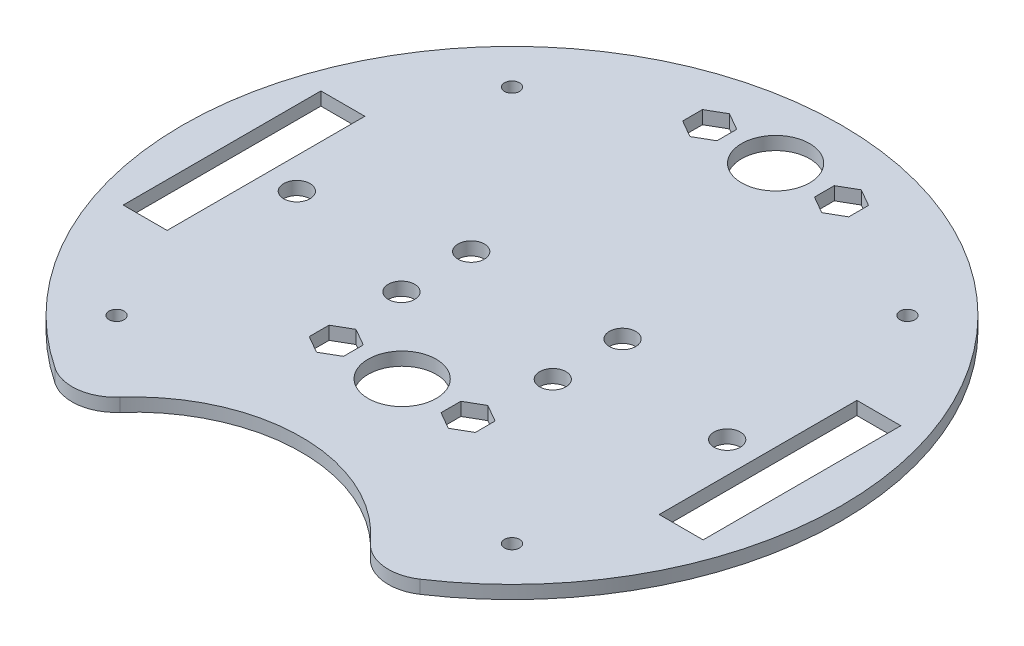
SolidWorks part; units mm, degrees
ref_plane "Front" through (0, 0, 0) normal (0, 0, 1) x (1, 0, 0)
ref_plane "Top" through (0, 0, 0) normal (0, 1, 0) x (1, 0, 0)
ref_plane "Right" through (0, 0, 0) normal (1, 0, 0) x (0, 0, -1)
sketch "Sketch1" plane through (0, 0, 0) normal (0, 1, 0) x (1, 0, 0)
  circle A0 centre (0, 0) radius 75
  dimension "D1" = 150
extrude "Boss-Extrude1" add sketch "Sketch1" along normal blind 3
sketch "Sketch2" plane through (0, 3, 0) normal (0, 1, 0) x (1, 0, 0)
  line L0 (-75, 0) -> (75, 0) construction
  line L2 (-66, -22.5) -> (-56, -22.5)
  line L3 (-66, -22.5) -> (-66, 22.5)
  line L4 (-66, 22.5) -> (-56, 22.5)
  line L5 (-56, -22.5) -> (-56, 22.5)
  line L6 (-66, -22.5) -> (-56, 22.5) construction
  line L7 (-66, 22.5) -> (-56, -22.5) construction
  line L8 (56, -22.5) -> (66, -22.5)
  line L9 (56, -22.5) -> (56, 22.5)
  line L10 (56, 22.5) -> (66, 22.5)
  line L11 (66, -22.5) -> (66, 22.5)
  line L12 (56, -22.5) -> (66, 22.5) construction
  line L13 (56, 22.5) -> (66, -22.5) construction
  circle A0 centre (0, 0) radius 75 construction
  point P5 (-61, 0)
  point P10 (61, 0)
  dimension "D1" = 45
  dimension "D2" = 45
  dimension "D3" = 10
  dimension "D4" = 10
  dimension "D5" = 61
  dimension "D6" = 61
extrude "Cut-Extrude1" cut sketch "Sketch2" against normal blind 6.35
sketch "Sketch3" plane through (0, 3, 0) normal (0, 1, 0) x (1, 0, 0)
  line L0 (0, 60) -> (0, -25) construction
  circle A0 centre (0, -25) radius 7.75
  circle A8 centre (0, 60) radius 7.75
  dimension "D1" = 15.5
  dimension "D2" = 15.5
  dimension "D6" = 60
  dimension "D7" = 25
extrude "Cut-Extrude2" cut sketch "Sketch3" against normal blind 10
sketch "Sketch4" plane through (0, 3, 0) normal (0, 1, 0) x (1, 0, 0)
  line L0 (0, 0) -> (0, -86.0323) construction
  line L1 (0, -86.0323) -> (33.1606, -67.2709) construction
  line L3 (-33.1606, -67.2709) -> (0, -86.0323) construction
  circle A0 centre (0, -86.0323) radius 38.1 construction
  circle A1 centre (0, 0) radius 75 construction
  arc A2 (-33.1606, -67.2709) -> (33.1606, -67.2709) centre (0, -86.0323) cw
  arc A3 (-33.1606, -67.2709) -> (33.1606, -67.2709) centre (0, 0) ccw
  dimension "D1" = 76.2
  dimension "D2" = 121
extrude "Cut-Extrude3" cut sketch "Sketch4" against normal blind 10 contours A2 A3
fillet "Fillet2" radius 10 2 edges at (33.1606, 1.5, 67.2709) (-33.1606, 1.5, 67.2709)
sketch "Sketch6" plane through (0, 3, 0) normal (0, 1, 0) x (1, 0, 0)
  line L0 (-15, 60) -> (15, 60) construction
  line L1 (0, 60) -> (0, 67.75) construction
  line L2 (0, 60) -> (0, 52.25) construction
  line L3 (0, -17.25) -> (0, -25) construction
  line L4 (0, -25) -> (0, -32.75) construction
  line L5 (-15, -25) -> (15, -25) construction
  line L6 (0, -17.25) -> (0, 0) construction
  line L7 (-15, 64.5021) -> (-18.8989, 62.251)
  line L8 (-18.8989, 62.251) -> (-18.8989, 57.749)
  line L9 (-18.8989, 57.749) -> (-15, 55.4979)
  line L10 (-15, 55.4979) -> (-11.1011, 57.749)
  line L11 (-11.1011, 57.749) -> (-11.1011, 62.251)
  line L12 (-11.1011, 62.251) -> (-15, 64.5021)
  line L13 (15, 64.5021) -> (11.1011, 62.251)
  line L14 (11.1011, 62.251) -> (11.1011, 57.749)
  line L15 (11.1011, 57.749) -> (15, 55.4979)
  line L16 (15, 55.4979) -> (18.8989, 57.749)
  line L17 (18.8989, 57.749) -> (18.8989, 62.251)
  line L18 (18.8989, 62.251) -> (15, 64.5021)
  line L19 (-15, -20.4979) -> (-18.8989, -22.749)
  line L20 (-18.8989, -22.749) -> (-18.8989, -27.251)
  line L21 (-18.8989, -27.251) -> (-15, -29.5021)
  line L22 (-15, -29.5021) -> (-11.1011, -27.251)
  line L23 (-11.1011, -27.251) -> (-11.1011, -22.749)
  line L24 (-11.1011, -22.749) -> (-15, -20.4979)
  line L25 (15, -20.4979) -> (11.1011, -22.749)
  line L26 (11.1011, -22.749) -> (11.1011, -27.251)
  line L27 (11.1011, -27.251) -> (15, -29.5021)
  line L28 (15, -29.5021) -> (18.8989, -27.251)
  line L29 (18.8989, -27.251) -> (18.8989, -22.749)
  line L30 (18.8989, -22.749) -> (15, -20.4979)
  line L31 (0, 52.25) -> (0, 0) construction
  circle A0 centre (-15, 60) radius 3.8989 construction
  circle A1 centre (15, 60) radius 3.8989 construction
  circle A6 centre (-15, -25) radius 3.8989 construction
  circle A7 centre (15, -25) radius 3.8989 construction
  circle A8 centre (0, -25) radius 7.75 construction
  circle A9 centre (0, 60) radius 7.75 construction
  dimension "D1" = 7.7978
  dimension "D3" = 7.7978
  dimension "D2" = 30
  dimension "D4" = 30
  dimension "D5" = 7.7978
  dimension "D6" = 7.7978
sketch "Sketch7" plane through (0, 3, 0) normal (0, 1, 0) x (1, 0, 0)
  line L0 (0, 75) -> (0, -47.9323) construction
  line L1 (-58.5, 0) -> (-48.975, 0) construction
  line L2 (17.225, 7.9375) -> (17.225, -7.9375) construction
  line L3 (-48.975, 0) -> (-17.225, 0) construction
  line L4 (-17.225, 7.9375) -> (-17.225, -7.9375) construction
  line L5 (-56, -22.5) -> (-56, 22.5) construction
  line L6 (48.975, 0) -> (17.225, 0) construction
  line L7 (58.5, 0) -> (48.975, 0) construction
  arc A0 (41.5307, -62.4516) -> (-41.5307, -62.4516) centre (0, 0) ccw construction
  arc A1 (28.5103, -60.7583) -> (-28.5103, -60.7583) centre (0, -86.0323) ccw construction
  circle A2 centre (-48.975, 0) radius 3
  circle A3 centre (-17.225, -7.9375) radius 3
  circle A4 centre (-17.225, 7.9375) radius 3
  circle A5 centre (17.225, 7.9375) radius 3
  circle A6 centre (17.225, -7.9375) radius 3
  circle A7 centre (48.975, 0) radius 3
  dimension "D1" = 6
  dimension "D2" = 9.525
  dimension "D3" = 31.75
  dimension "D4" = 15.875
  dimension "D5" = 2.5
extrude "Cut-Extrude5" cut sketch "Sketch7" against normal blind 3
extrude "Cut-Extrude6" cut sketch "Sketch6" against normal blind 3
sketch "Sketch8" plane through (0, 0, 0) normal (0, -1, 0) x (-1, 0, 0)
  line L1 (45, 45) -> (-45, 45) construction
  line L2 (45, 45) -> (45, -45) construction
  line L3 (45, -45) -> (-45, -45) construction
  line L4 (-45, 45) -> (-45, -45) construction
  line L5 (45, 45) -> (-45, -45) construction
  line L6 (45, -45) -> (-45, 45) construction
  circle A0 centre (45, -45) radius 1.7145
  circle A1 centre (-45, -45) radius 1.7145
  circle A2 centre (-45, 45) radius 1.7145
  circle A3 centre (45, 45) radius 1.7145
  point P0 (0, 0)
  dimension "D3" = 3.429
  dimension "D1" = 90
  dimension "D2" = 90
extrude "Cut-Extrude7" cut sketch "Sketch8" against normal blind 10
